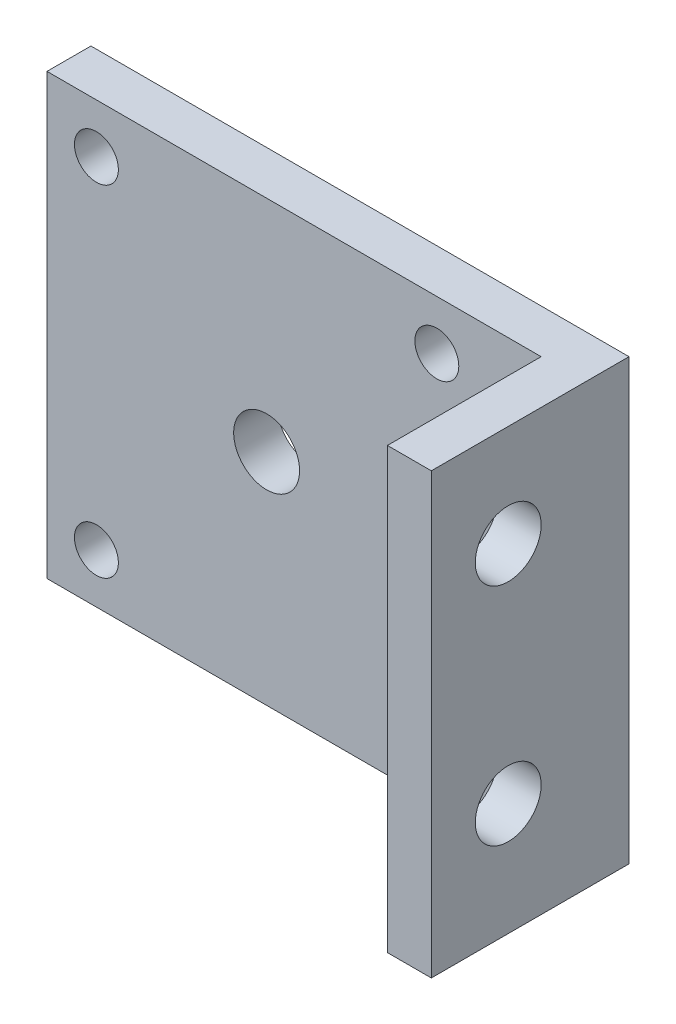
SolidWorks part; units mm, degrees
ref_plane "Plan de face" through (0, 0, 0) normal (0, 0, 1) x (1, 0, 0)
ref_plane "Plan de dessus" through (0, 0, 0) normal (0, 1, 0) x (1, 0, 0)
ref_plane "Plan de droite" through (0, 0, 0) normal (1, 0, 0) x (0, 0, -1)
sketch "Esquisse1" plane through (0, 0, 0) normal (0, 0, 1) x (1, 0, 0)
  line L1 (-27.0859, 17.2904) -> (21.9141, 17.2904)
  line L2 (-27.0859, 17.2904) -> (-27.0859, -22.7096)
  line L3 (-27.0859, -22.7096) -> (21.9141, -22.7096)
  line L4 (21.9141, 17.2904) -> (21.9141, -22.7096)
  dimension "D1" = 49
  dimension "D2" = 40
extrude "Boss.-Extru.1" add sketch "Esquisse1" along normal blind 4
sketch "Esquisse2" plane through (0, 0, 4) normal (0, 0, 1) x (1, 0, 0)
  line L0 (-27.0859, -22.7096) -> (21.9141, -22.7096) construction
  line L1 (21.9141, 17.2904) -> (17.9141, 17.2904)
  line L2 (21.9141, 17.2904) -> (21.9141, -22.7096)
  line L3 (21.9141, -22.7096) -> (17.9141, -22.7096)
  line L4 (17.9141, 17.2904) -> (17.9141, -22.7096)
  dimension "D1" = 4
extrude "Boss.-Extru.2" add sketch "Esquisse2" along normal blind 14
sketch "Esquisse3" plane through (21.9141, 0, 0) normal (1, 0, 0) x (0, 0, -1)
  line L0 (-18, -22.7096) -> (0, -22.7096) construction
  line L1 (-11, 17.2904) -> (-11, -23.7096) construction
  line L3 (-18, -22.7096) -> (-18, 17.2904) construction
  circle A0 centre (-11, 8.0404) radius 3
  circle A1 centre (-11, -12.4596) radius 3
  dimension "D1" = 6
  dimension "D2" = 6
  dimension "D3" = 20.5
  dimension "D4" = 10.25
  dimension "D5" = 7
extrude "Enlèv. mat.-Extru.1" cut sketch "Esquisse3" against normal blind 4
sketch "Esquisse4" plane through (0, 0, 4) normal (0, 0, 1) x (1, 0, 0)
  line L0 (-7.0859, 17.2904) -> (-7.0859, -22.7096) construction
  line L2 (-27.0859, -22.7096) -> (17.9141, -22.7096) construction
  line L3 (-27.0859, -2.7096) -> (17.9141, -2.7096) construction
  line L4 (-27.0859, 17.2904) -> (-27.0859, -22.7096) construction
  line L5 (17.9141, 17.2904) -> (17.9141, -22.7096) construction
  circle A0 centre (-7.0859, -2.7096) radius 3
  circle A1 centre (-22.5859, 12.7904) radius 2
  circle A2 centre (8.4141, 12.7904) radius 2
  circle A3 centre (8.4141, -18.2096) radius 2
  circle A4 centre (-22.5859, -18.2096) radius 2
  dimension "D1" = 6
  dimension "D6" = 4
  dimension "D7" = 4
  dimension "D8" = 4
  dimension "D9" = 4
  dimension "D2" = 31
  dimension "D3" = 4.5
  dimension "D4" = 31
  dimension "D5" = 4.5
  dimension "D10" = 20
extrude "Enlèv. mat.-Extru.2" cut sketch "Esquisse4" against normal through all
